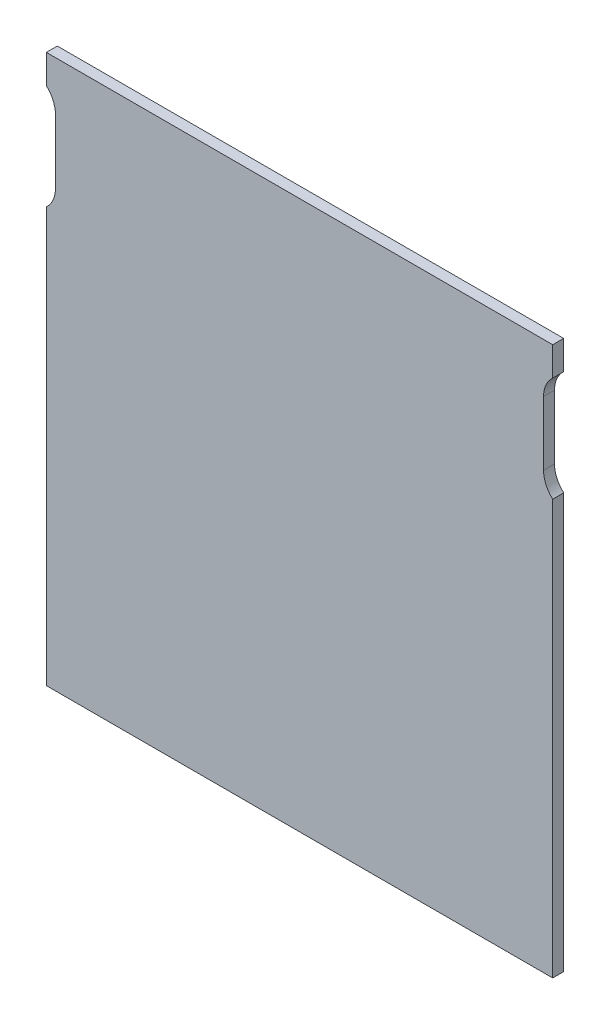
SolidWorks part; units mm, degrees
ref_plane "Front" through (0, 0, 0) normal (0, 0, 1) x (1, 0, 0)
ref_plane "Top" through (0, 0, 0) normal (0, 1, 0) x (1, 0, 0)
ref_plane "Right" through (0, 0, 0) normal (1, 0, 0) x (0, 0, -1)
sketch "Sketch1" plane through (0, 0, 0) normal (0, 0, 1) x (1, 0, 0)
  line L0 (-138.5, -150) -> (-138.5, 150)
  line L1 (-138.5, -150) -> (138.5, -150)
  line L2 (-138.5, 150) -> (138.5, 150)
  line L3 (138.5, -150) -> (138.5, 150)
  line L4 (-138.5, -150) -> (138.5, 150) construction
  line L5 (-138.5, 150) -> (138.5, -150) construction
  point P1 (0, 0)
  dimension "D1" = 300
  dimension "D2" = 277
extrude "Boss-Extrude1" add sketch "Sketch1" along normal blind 6 contours L0 L1 L3 L2
sketch "Sketch2" plane through (0, 0, 6) normal (0, 0, 1) x (1, 0, 0)
  line L0 (138.5, -150) -> (138.5, 150) construction
  line L3 (-138.5, 150) -> (138.5, 150) construction
  line L7 (148.5, 123) -> (148.5, 88) construction
  line L8 (133.5, 123) -> (133.5, 88)
  line L9 (163.5, 123) -> (163.5, 88)
  arc A2 (133.5, 123) -> (163.5, 123) centre (148.5, 123) cw
  arc A3 (163.5, 88) -> (133.5, 88) centre (148.5, 88) cw
  point P19 (148.5, 105.5)
  point P24 (148.5, 73)
  point P25 (148.5, 138)
  dimension "D1" = 65
  dimension "D2" = 30
  dimension "D3" = 5
  dimension "D4" = 12
sketch "Sketch3" plane through (0, 0, 0) normal (0, 0, -1) x (-1, 0, 0)
  line L0 (-103.5, -130) -> (-34.218, -140)
  line L1 (-103.5, -130) -> (-102.0714, -120.1026)
  line L2 (-34.218, -140) -> (-32.7894, -130.1026)
  line L3 (-102.0714, -120.1026) -> (-32.7894, -130.1026)
  line L4 (-103.5, -130) -> (-32.7894, -130.1026) construction
  line L5 (-34.218, -140) -> (-102.0714, -120.1026) construction
  line L6 (138.5, -150) -> (-138.5, -150) construction
  line L7 (-138.5, -150) -> (-138.5, 150) construction
  point P1 (-68.1447, -130.0513)
  dimension "D1" = 70
  dimension "D2" = 10
  dimension "D3" = 10
  dimension "D4" = 20
  dimension "D5" = 35
extrude "Boss-Extrude2" add sketch "Sketch3" along normal blind 7
sketch "Sketch4" plane through (0, 0, -7) normal (0, 0, -1) x (-1, 0, 0)
  line L0 (-102.0714, -120.1026) -> (-32.7894, -130.1026)
  line L1 (-102.0714, -120.1026) -> (-104.2143, -134.9487)
  line L2 (-32.7894, -130.1026) -> (-34.9323, -144.9487)
  line L3 (-104.2143, -134.9487) -> (-34.9323, -144.9487)
  line L4 (-34.218, -140) -> (-32.7894, -130.1026) construction
  line L5 (-32.7894, -130.1026) -> (-102.0714, -120.1026) construction
  dimension "D1" = 15
extrude "Boss-Extrude3" add sketch "Sketch4" along normal blind 5
extrude "Cut-Extrude1" cut sketch "Sketch2" against normal through all
mirror "Mirror1" about plane through (0, 0, 0) normal (1, 0, 0) of "Boss-Extrude3", "Cut-Extrude1", "Boss-Extrude2"
